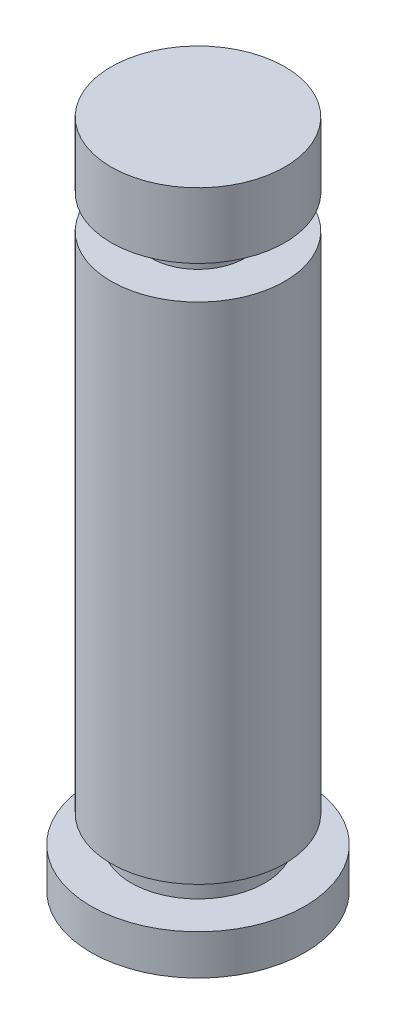
SolidWorks part; units mm, degrees
ref_plane "Front Plane" through (0, 0, 0) normal (0, 0, 1) x (1, 0, 0)
ref_plane "Top Plane" through (0, 0, 0) normal (0, 1, 0) x (1, 0, 0)
ref_plane "Right Plane" through (0, 0, 0) normal (1, 0, 0) x (0, 0, -1)
sketch "Sketch1" plane through (0, 0, 0) normal (0, 0, 1) x (1, 0, 0)
  line L0 (0, 0) -> (0, 56.7893) construction
  line L1 (0, 0) -> (-8, 0)
  line L2 (-8, 0) -> (-8, 3)
  line L3 (-8, 3) -> (-5, 3)
  line L4 (-5, 3) -> (-5, 5)
  line L5 (-5, 5) -> (-6.4925, 5)
  line L6 (-6.4925, 5) -> (-6.4925, 42.7)
  line L7 (-6.4925, 42.7) -> (-3.5, 42.7)
  line L8 (-3.5, 42.7) -> (-3.5, 45.2)
  line L9 (-3.5, 45.2) -> (-6.4925, 45.2)
  line L10 (-6.4925, 45.2) -> (-6.4925, 50.1)
  line L11 (-6.4925, 50.1) -> (0, 50.1)
  line L12 (0, 0) -> (0, 50.1)
  point P16 (-6.5, 3)
  point P17 (-4.9963, 42.7)
  dimension "D1" = 3
  dimension "D2" = 2
  dimension "D3" = 4.9
  dimension "D4" = 2.5
  dimension "D5" = 7
  dimension "D6" = 10
  dimension "D7" = 12.985
  dimension "D8" = 8
  dimension "D9" = 50.1
revolve "Revolve1" add sketch "Sketch1" angle 360 about L0
